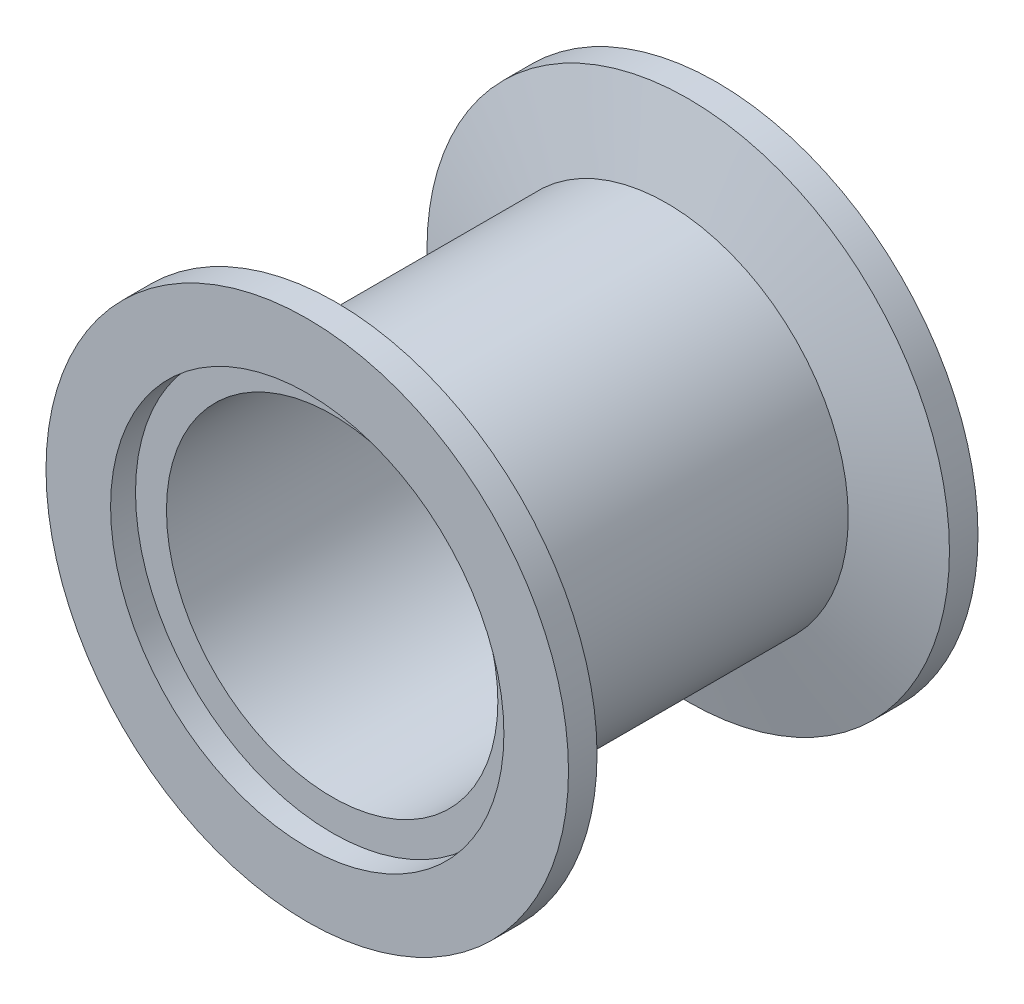
SolidWorks part; units mm, degrees
ref_plane "Front Plane" through (0, 0, 0) normal (0, 0, 1) x (1, 0, 0)
ref_plane "Top Plane" through (0, 0, 0) normal (0, 1, 0) x (1, 0, 0)
ref_plane "Right Plane" through (0, 0, 0) normal (1, 0, 0) x (0, 0, -1)
sketch "Sketch1" plane through (0, 0, 0) normal (1, 0, 0) x (0, 0, -1)
  line L0 (-21.5, 0) -> (21.5, 0) construction
  line L1 (-21.5, -27.432) -> (-21.5, 27.432) construction
  line L2 (21.5, -27.432) -> (21.5, 27.432) construction
  line L3 (-21.5, 17.399) -> (21.5, 17.399) construction
  line L4 (-21.5, 20.6502) -> (-18.8838, 20.6502) construction
  line L5 (-21.5, -17.399) -> (21.5, -17.399) construction
  line L6 (-18.8838, 20.6502) -> (-18.8838, -20.6502) construction
  line L7 (-18.8838, -20.6502) -> (-21.5, -20.6502) construction
  line L8 (-21.5, 27.432) -> (-18.5028, 27.432) construction
  line L9 (-18.5028, 27.432) -> (-16.2568, 19.05) construction
  line L10 (-16.2568, 19.05) -> (21.5, 19.05) construction
  line L11 (21.5, 27.432) -> (18.5028, 27.432) construction
  line L12 (18.5028, 27.432) -> (16.2568, 19.05) construction
  point P7 (21.5, 19.05)
  point P8 (21.5, -19.05)
  point P21 (-18.8838, 0)
  dimension "D1" = 105
  dimension "Length" = 43
  dimension "Flange OD" = 54.864
  dimension "For Tube OD" = 38.1
  dimension "ID" = 34.798
  dimension "Connection ID" = 41.3004
  dimension "Connection Depth" = 2.6162
  dimension "Flange Flat Thickness" = 2.9972
sketch "Sketch2" plane through (0, 0, 0) normal (1, 0, 0) x (0, 0, -1)
  line L0 (21.5, -27.432) -> (21.5, 27.432) construction
  line L1 (21.5, 27.432) -> (18.5028, 27.432) construction
  line L2 (18.5028, 27.432) -> (16.2568, 19.05) construction
  line L3 (-21.5, 27.432) -> (-18.5028, 27.432) construction
  line L4 (-18.5028, 27.432) -> (-16.2568, 19.05) construction
  line L5 (-16.2568, 19.05) -> (21.5, 19.05) construction
  line L6 (-21.5, 17.399) -> (21.5, 17.399) construction
  line L7 (-21.5, 20.6502) -> (-18.8838, 20.6502) construction
  line L8 (-21.5, -27.432) -> (-21.5, 27.432) construction
  line L9 (21.5, 20.6502) -> (21.5, 27.432)
  line L10 (21.5, 27.432) -> (18.5028, 27.432)
  line L11 (18.5028, 27.432) -> (16.2568, 19.05)
  line L12 (-21.5, 27.432) -> (-18.5028, 27.432)
  line L13 (-18.5028, 27.432) -> (-16.2568, 19.05)
  line L14 (-16.2568, 19.05) -> (16.2568, 19.05)
  line L15 (-18.8838, 17.399) -> (18.8838, 17.399)
  line L16 (-21.5, 20.6502) -> (-18.8838, 20.6502)
  line L17 (-21.5, 20.6502) -> (-21.5, 27.432)
  line L18 (-18.8838, 20.6502) -> (-18.8838, -20.6502) construction
  line L19 (-18.8838, 20.6502) -> (-18.8838, 17.399)
  line L20 (18.8838, 17.399) -> (18.8838, 20.6502)
  line L21 (18.8838, 20.6502) -> (21.5, 20.6502)
revolve "Revolve1" add sketch "Sketch2" angle 360 about L0
